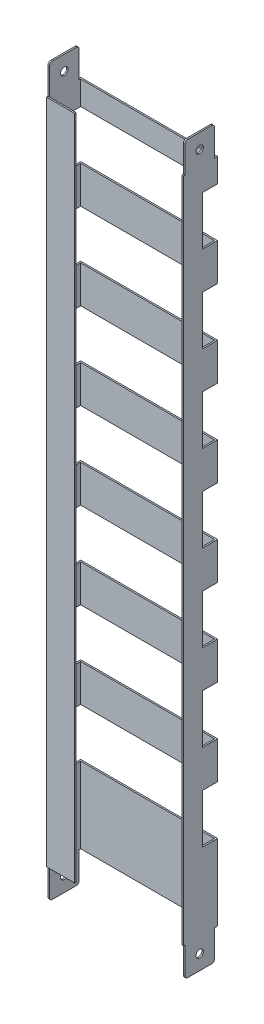
SolidWorks part; units mm, degrees
ref_plane "Front Plane" through (0, 0, 0) normal (0, 0, 1) x (1, 0, 0)
ref_plane "Top Plane" through (0, 0, 0) normal (0, 1, 0) x (1, 0, 0)
ref_plane "Right Plane" through (0, 0, 0) normal (1, 0, 0) x (0, 0, -1)
sketch "Sketch1" plane through (0, 0, 0) normal (0, 1, 0) x (1, 0, 0)
  line L0 (0, 0) -> (0, 1)
  line L1 (0, 1) -> (-18, 1)
  line L2 (-18, 1) -> (-18, 22)
  line L3 (-18, 22) -> (72, 22)
  line L4 (72, 22) -> (72, 0)
  line L5 (72, 0) -> (73, 0)
  line L6 (73, 0) -> (73, 23)
  line L7 (73, 23) -> (-19, 23)
  line L8 (-19, 23) -> (-19, 0)
  line L9 (-19, 0) -> (0, 0)
  dimension "D1" = 1
  dimension "D2" = 1
  dimension "D3" = 1
  dimension "D4" = 1
  dimension "D5" = 23
  dimension "D6" = 92
  dimension "D7" = 19
extrude "Boss-Extrude1" add sketch "Sketch1" along normal blind 448
sketch "Sketch2" plane through (0, 448, 0) normal (0, 1, 0) x (1, 0, 0)
  line L0 (-19, 23) -> (-19, 0) construction
  line L1 (-18, 1) -> (-19, 1)
  line L2 (-18, 1) -> (-18, 21)
  line L3 (-18, 21) -> (-19, 21)
  line L4 (-19, 1) -> (-19, 21)
  line L5 (72, 22) -> (72, 0) construction
  line L6 (72, 1) -> (73, 1)
  line L7 (72, 1) -> (72, 21)
  line L8 (72, 21) -> (73, 21)
  line L9 (73, 1) -> (73, 21)
  line L10 (73, 0) -> (73, 23) construction
  line L11 (73, 23) -> (-19, 23) construction
  dimension "D1" = 2
  dimension "D2" = 2
extrude "Boss-Extrude2" add sketch "Sketch2" along normal blind 20
sketch "Sketch3" plane through (0, 0, 0) normal (0, -1, 0) x (-1, 0, 0)
  line L0 (19, 23) -> (19, 0) construction
  line L1 (18, 1) -> (19, 1)
  line L2 (18, 1) -> (18, 21)
  line L3 (18, 21) -> (19, 21)
  line L4 (19, 1) -> (19, 21)
  line L5 (-73, 0) -> (-73, 23) construction
  line L6 (-72, 1) -> (-73, 1)
  line L7 (-72, 1) -> (-72, 21)
  line L8 (-72, 21) -> (-73, 21)
  line L9 (-73, 1) -> (-73, 21)
  line L10 (-73, 23) -> (19, 23) construction
  dimension "D1" = 2
extrude "Boss-Extrude3" add sketch "Sketch3" along normal blind 20
fillet "Fillet1" radius 2 8 edges at (72.5, 468, -21) (72.5, 468, -1) (-18.5, 468, -1) (-18.5, 468, -21) (72.5, -20, -21) (72.5, -20, -1) (-18.5, -20, -1) (-18.5, -20, -21)
sketch "Sketch4" plane through (73, 0, 0) normal (1, 0, 0) x (0, 0, -1)
  line L0 (23, 448) -> (23, 0) construction
  line L1 (23, 432) -> (13, 432)
  line L2 (23, 432) -> (23, 399)
  line L3 (23, 399) -> (13, 399)
  line L4 (13, 432) -> (13, 399)
  line L5 (21, 448) -> (23, 448) construction
  dimension "D1" = 16
  dimension "D2" = 33
  dimension "D3" = 10
extrude "Cut-Extrude1" cut sketch "Sketch4" against normal through all
pattern_linear "LPattern1" count 7 spacing 58 along (0, -1, 0) of "Cut-Extrude1"
sketch "Sketch5" plane through (73, 0, 0) normal (1, 0, 0) x (0, 0, -1)
  line L0 (3, 468) -> (19, 468) construction
  line L1 (19, -20) -> (3, -20) construction
  circle A0 centre (11, 458) radius 2.5
  circle A1 centre (11, -10) radius 2.5
  dimension "D1" = 5
  dimension "D3" = 5
  dimension "D2" = 10
  dimension "D4" = 10
extrude "Cut-Extrude2" cut sketch "Sketch5" against normal through all
